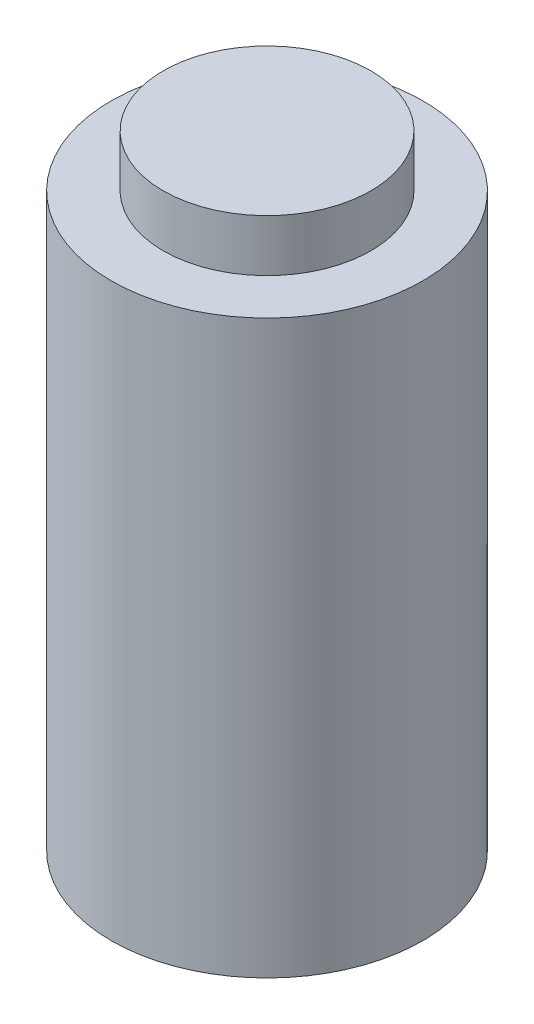
SolidWorks part; units mm, degrees
ref_plane "Front Plane" through (0, 0, 0) normal (0, 0, 1) x (1, 0, 0)
ref_plane "Top Plane" through (0, 0, 0) normal (0, 1, 0) x (1, 0, 0)
ref_plane "Right Plane" through (0, 0, 0) normal (1, 0, 0) x (0, 0, -1)
sketch "Sketch1" plane through (0, 0, 0) normal (0, 1, 0) x (1, 0, 0)
  circle A0 centre (0, 0) radius 38.1
  dimension "D1" = 76.2
extrude "Boss-Extrude5" add sketch "Sketch1" along normal blind 139.7
sketch "Sketch3" plane through (0, 139.7, 0) normal (0, 1, 0) x (1, 0, 0)
  circle A0 centre (0, 0) radius 25.4
  dimension "D1" = 50.8
extrude "Boss-Extrude6" add sketch "Sketch3" along normal blind 12.7
